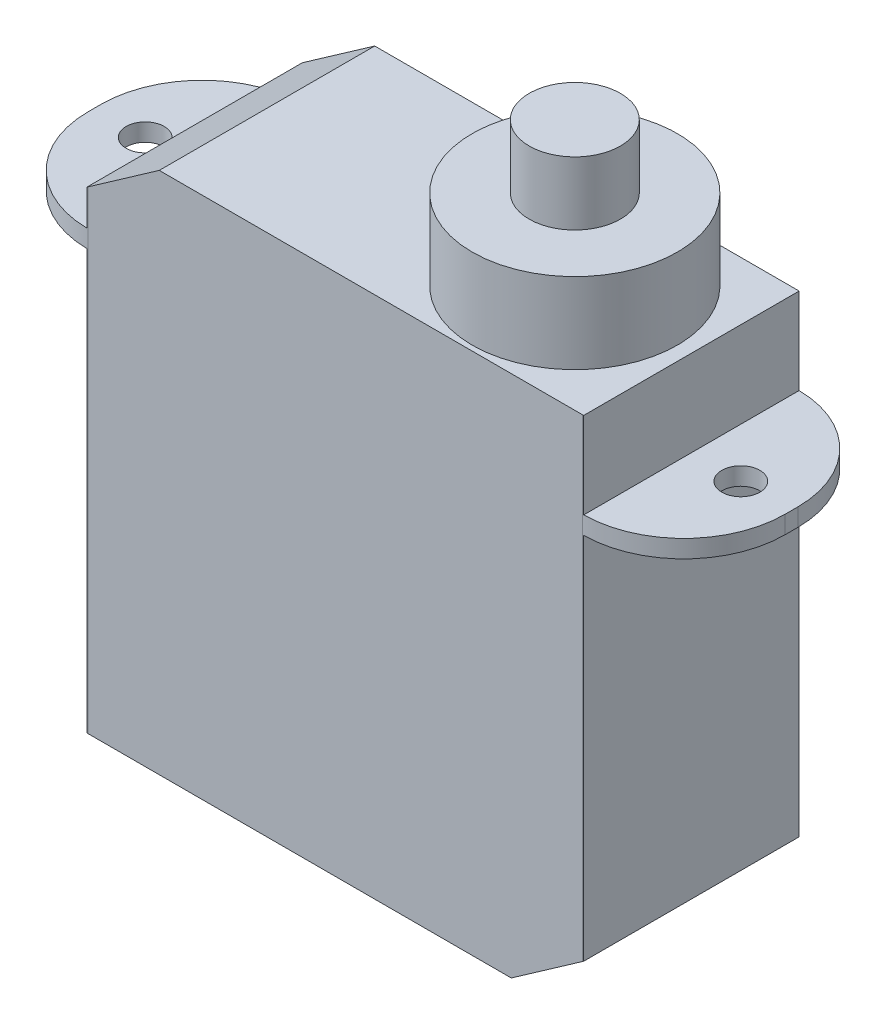
SolidWorks part; units mm, degrees
ref_plane "Front Plane" through (0, 0, 0) normal (0, 0, 1) x (1, 0, 0)
ref_plane "Top Plane" through (0, 0, 0) normal (0, 1, 0) x (1, 0, 0)
ref_plane "Right Plane" through (0, 0, 0) normal (1, 0, 0) x (0, 0, -1)
sketch "Sketch1" plane through (0, 0, 0) normal (0, 1, 0) x (1, 0, 0)
  line L1 (-9.8, 4.25) -> (9.8, 4.25)
  line L2 (-9.8, 4.25) -> (-9.8, -4.25)
  line L3 (-9.8, -4.25) -> (9.8, -4.25)
  line L4 (9.8, 4.25) -> (9.8, -4.25)
  line L5 (-9.8, 4.25) -> (9.8, -4.25) construction
  line L6 (-9.8, -4.25) -> (9.8, 4.25) construction
  point P0 (0, 0)
  dimension "D1" = 19.6
  dimension "D2" = 8.5
extrude "Boss-Extrude1" add sketch "Sketch1" against normal blind 17.25 and the other way blind 3.4
sketch "Sketch2" plane through (0, 3.4, 0) normal (0, 1, 0) x (1, 0, 0)
  line L0 (-9.8, 4.25) -> (-9.8, -4.25) construction
  circle A0 centre (5.2, 0) radius 4.05
  dimension "D1" = 8.1
  dimension "D2" = 15
extrude "Boss-Extrude2" add sketch "Sketch2" along normal blind 3.18
sketch "Sketch4" plane through (0, 0, 0) normal (0, 1, 0) x (1, 0, 0)
  line L0 (9.8, -4.25) -> (9.8, 4.25) construction
  line L1 (9.8, 4.25) -> (13.75, 4.25)
  line L2 (9.8, 4.25) -> (9.8, -4.25)
  line L3 (9.8, -4.25) -> (13.75, -4.25)
  line L4 (13.75, 4.25) -> (13.75, -4.25)
  line L5 (-9.8, -4.25) -> (9.8, -4.25) construction
  line L6 (9.8, 4.25) -> (-9.8, 4.25) construction
  line L7 (-9.8, 4.25) -> (-9.8, -4.25) construction
  line L8 (-9.8, 4.25) -> (-13.75, 4.25)
  line L9 (-9.8, 4.25) -> (-9.8, -4.25)
  line L10 (-9.8, -4.25) -> (-13.75, -4.25)
  line L11 (-13.75, 4.25) -> (-13.75, -4.25)
  line L12 (-11.75, 0) -> (11.75, 0) construction
  circle A0 centre (11.75, 0) radius 0.75
  circle A1 centre (-11.75, 0) radius 0.75
  dimension "D3" = 1.5
  dimension "D1" = 27.5
  dimension "D2" = 23.5
extrude "Boss-Extrude3" add sketch "Sketch4" against normal blind 0.7
fillet "Fillet1" radius 4 4 edges at (13.75, -0.35, -4.25) (13.75, -0.35, 4.25) (-13.75, -0.35, -4.25) (-13.75, -0.35, 4.25)
sketch "Sketch5" plane through (0, 6.58, 0) normal (0, 1, 0) x (1, 0, 0)
  circle A0 centre (5.2, 0) radius 1.8
  circle A1 centre (5.2, 0) radius 4.05 construction
  dimension "D1" = 3.6
extrude "Boss-Extrude4" add sketch "Sketch5" along normal blind 2.5
chamfer "Chamfer1" distance 2 angle 55 2 edges at (9.8, -17.25, 0) (-9.8, 3.4, 0)
